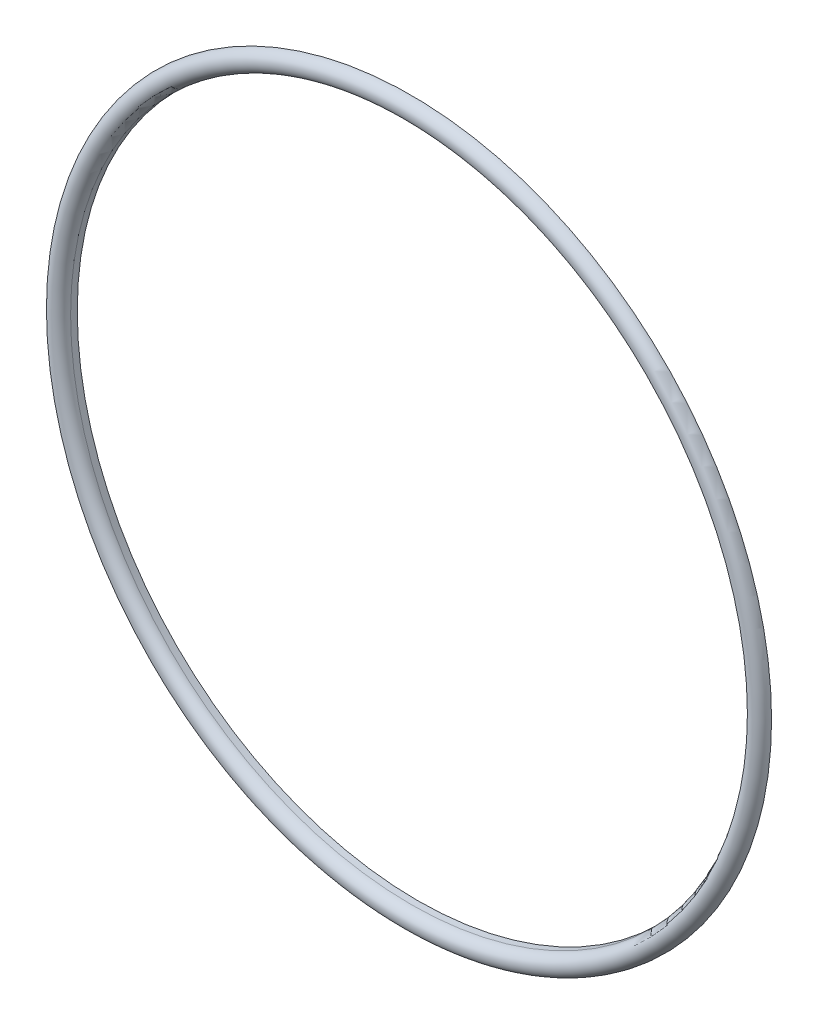
SolidWorks part; units mm, degrees
ref_plane "Front Plane" through (0, 0, 0) normal (0, 0, 1) x (1, 0, 0)
ref_plane "Top Plane" through (0, 0, 0) normal (0, 1, 0) x (1, 0, 0)
ref_plane "Right Plane" through (0, 0, 0) normal (1, 0, 0) x (0, 0, -1)
sketch "Sketch1" plane through (0, 0, 0) normal (0, 0, 1) x (1, 0, 0)
  circle A0 centre (0, 0) radius 52.5 construction
  circle A1 centre (0, 0) radius 52.5
sketch "Sketch2" plane through (0, 0, 0) normal (1, 0, 0) x (0, 0, -1)
  line L0 (0, 52.5) -> (0, -52.5) construction
  line L1 (0, 51) -> (0, -52.5) construction
  line L2 (0, 0) -> (-11.1408, 0) construction
  line L7 (0, 54) -> (0, 52.5)
  line L8 (0, 52.5) -> (1, 52.5)
  line L9 (1, 52.5) -> (1, 51)
  line L10 (1, 51) -> (0, 51)
  arc A0 (0, 54) -> (0, 51) centre (0, 52.5) ccw
  dimension "D1" = 3
  dimension "D2" = 1
revolve "Revolve1" add sketch "Sketch2" angle 360 about L2
